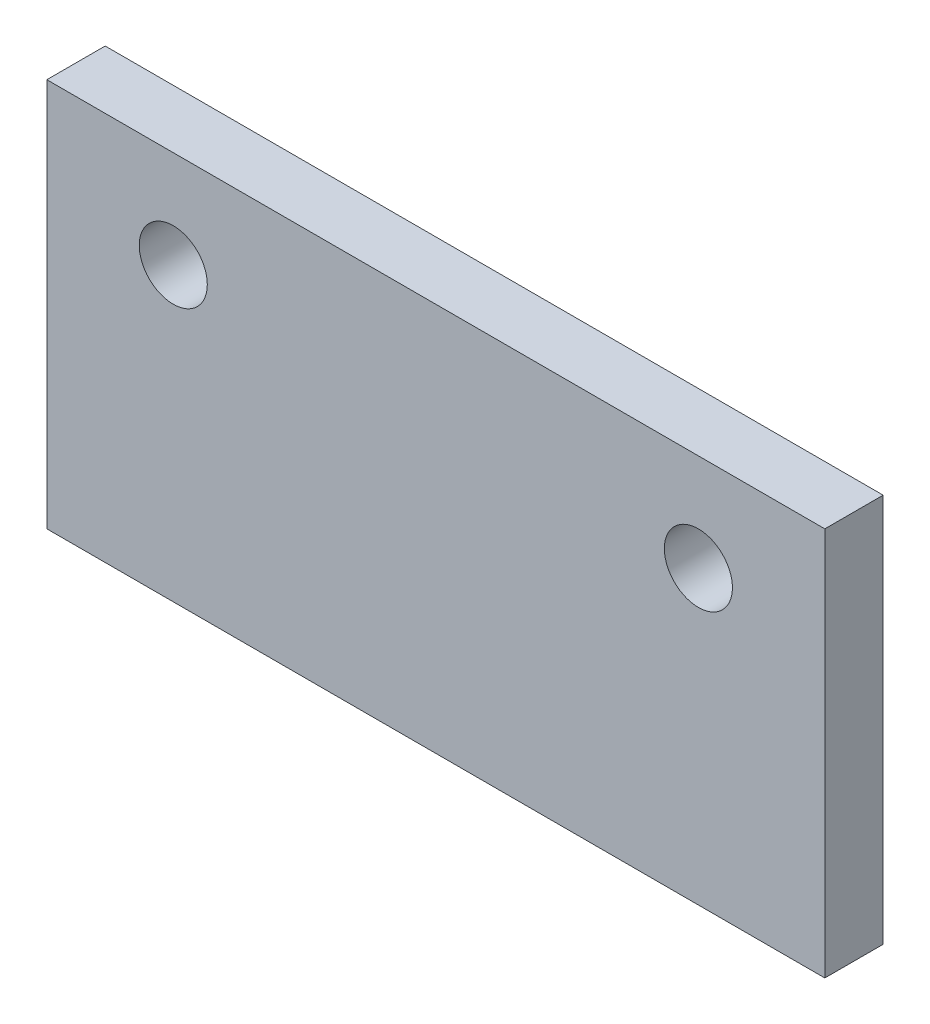
SolidWorks part; units mm, degrees
ref_plane "前基準面" through (0, 0, 0) normal (0, 0, 1) x (1, 0, 0)
ref_plane "上基準面" through (0, 0, 0) normal (0, 1, 0) x (1, 0, 0)
ref_plane "右基準面" through (0, 0, 0) normal (1, 0, 0) x (0, 0, -1)
sketch "草圖1" plane through (0, 0, 0) normal (0, 0, 1) x (1, 0, 0)
  line L0 (0, 10) -> (0, -10) construction
  line L1 (-20, 10) -> (20, 10)
  line L2 (-20, 10) -> (-20, -10)
  line L3 (-20, -10) -> (20, -10)
  line L4 (20, 10) -> (20, -10)
  circle A0 centre (-13.5, 5) radius 1.75
  circle A1 centre (13.5, 5) radius 1.75
  dimension "D3" = 5
  dimension "D4" = 6.5
  dimension "D5" = 3.5
  dimension "D1" = 20
  dimension "D2" = 40
extrude "填料-伸長1" add sketch "草圖1" along normal blind 3
